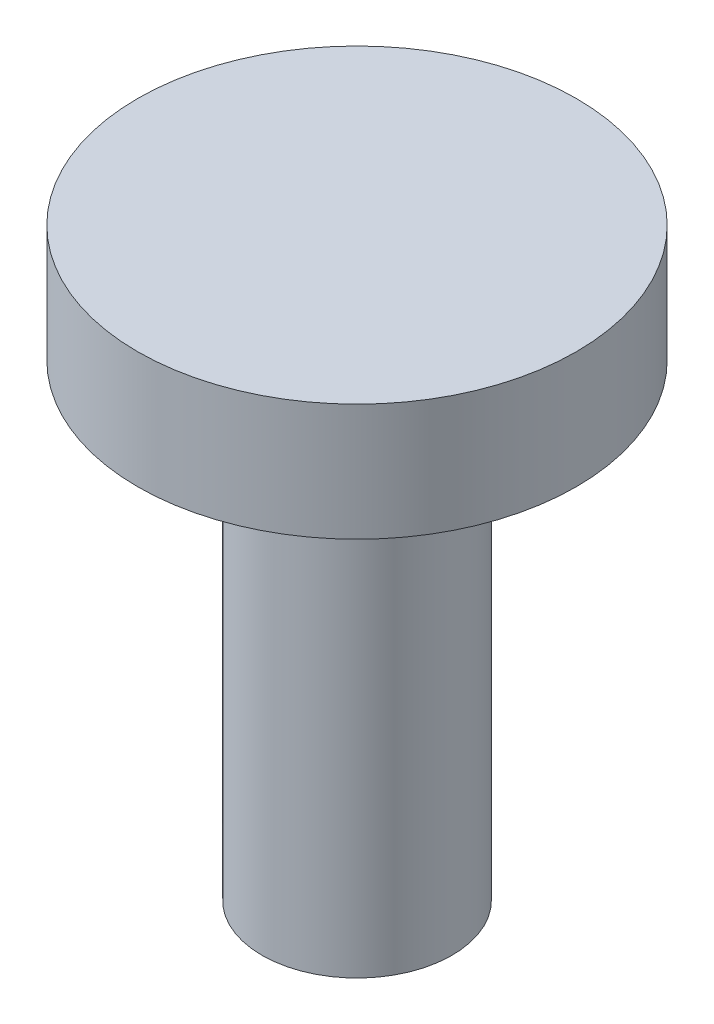
SolidWorks part; units mm, degrees
ref_plane "Спереди" through (0, 0, 0) normal (0, 0, 1) x (1, 0, 0)
ref_plane "Сверху" through (0, 0, 0) normal (0, 1, 0) x (1, 0, 0)
ref_plane "Справа" through (0, 0, 0) normal (1, 0, 0) x (0, 0, -1)
other "Configuration Table"
sketch "Эскиз1" plane through (0, 0, 0) normal (0, 1, 0) x (1, 0, 0)
  circle A0 centre (0, 0) radius 3.25
  dimension "D1" = 6.5
extrude "Бобышка-Вытянуть1" add sketch "Эскиз1" along normal blind 16 contours A0
sketch "Эскиз2" plane through (0, 16, 0) normal (0, 1, 0) x (1, 0, 0)
  circle A0 centre (0, 0) radius 7.5
  dimension "D1" = 15
extrude "Бобышка-Вытянуть2" add sketch "Эскиз2" along normal blind 4
